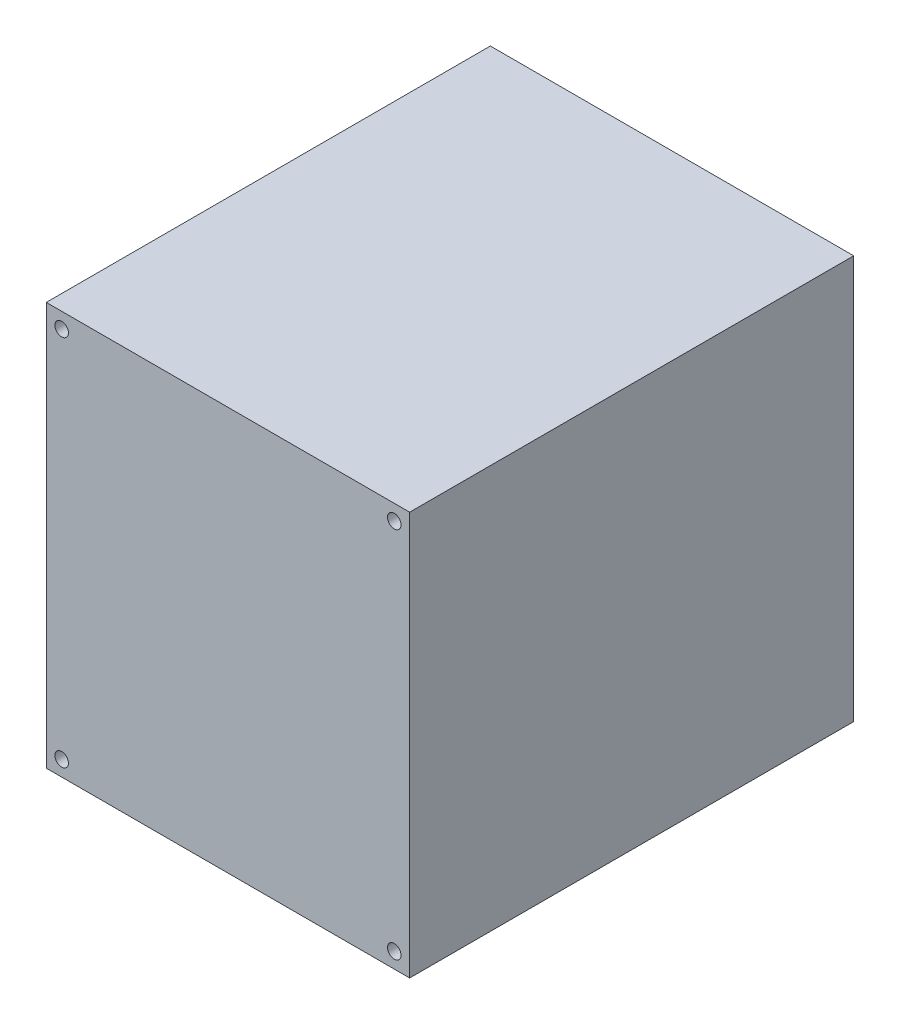
SolidWorks part; units mm, degrees
ref_plane "Front Plane" through (0, 0, 0) normal (0, 0, 1) x (1, 0, 0)
ref_plane "Top Plane" through (0, 0, 0) normal (0, 1, 0) x (1, 0, 0)
ref_plane "Right Plane" through (0, 0, 0) normal (1, 0, 0) x (0, 0, -1)
sketch "Sketch1" plane through (0, 0, 0) normal (0, 0, 1) x (1, 0, 0)
  line L1 (-59, -65.5) -> (59, -65.5)
  line L2 (-59, -65.5) -> (-59, 65.5)
  line L3 (-59, 65.5) -> (59, 65.5)
  line L4 (59, -65.5) -> (59, 65.5)
  line L5 (-59, -65.5) -> (59, 65.5) construction
  line L6 (-59, 65.5) -> (59, -65.5) construction
  point P0 (0, 0)
  dimension "D1" = 118
  dimension "D2" = 131
extrude "Boss-Extrude1" add sketch "Sketch1" along normal blind 144.2
sketch "Sketch2" plane through (0, 0, 0) normal (0, 0, -1) x (-1, 0, 0)
  line L0 (-54, -60.5) -> (-54, 60.5) construction
  line L1 (-54, 60.5) -> (54, 60.5) construction
  line L2 (54, 60.5) -> (54, -60.5) construction
  line L3 (54, -60.5) -> (-54, -60.5) construction
  line L4 (0, 60.5) -> (0, 0) construction
  line L5 (0, 0) -> (-54, 0) construction
  circle A0 centre (-54, 60.5) radius 2.2
  circle A1 centre (54, 60.5) radius 2.2
  circle A2 centre (54, -60.5) radius 2.2
  circle A3 centre (-54, -60.5) radius 2.2
  dimension "D3" = 4.4
  dimension "D1" = 108
  dimension "D2" = 121
extrude "Cut-Extrude1" cut sketch "Sketch2" against normal through all
